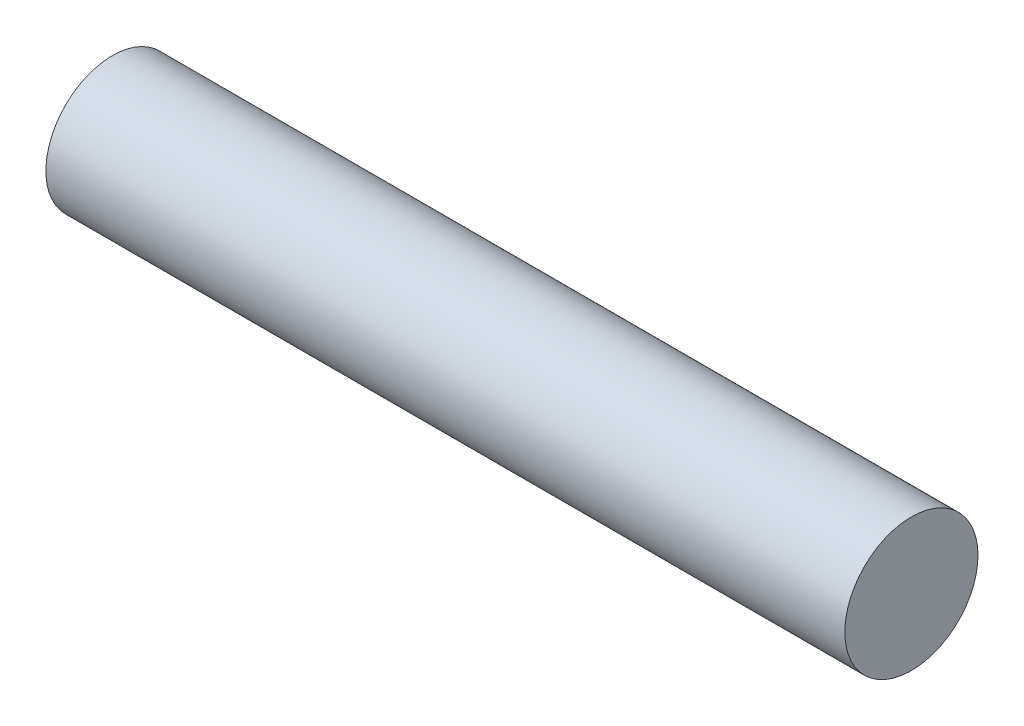
SolidWorks part; units mm, degrees
ref_plane "Front Plane" through (0, 0, 0) normal (0, 0, 1) x (1, 0, 0)
ref_plane "Top Plane" through (0, 0, 0) normal (0, 1, 0) x (1, 0, 0)
ref_plane "Right Plane" through (0, 0, 0) normal (1, 0, 0) x (0, 0, -1)
sketch "Sketch1" plane through (0, 0, 0) normal (1, 0, 0) x (0, 0, -1)
  circle A0 centre (0, 0) radius 5
  dimension "D1" = 10
extrude "Boss-Extrude1" add sketch "Sketch1" along normal blind 60
